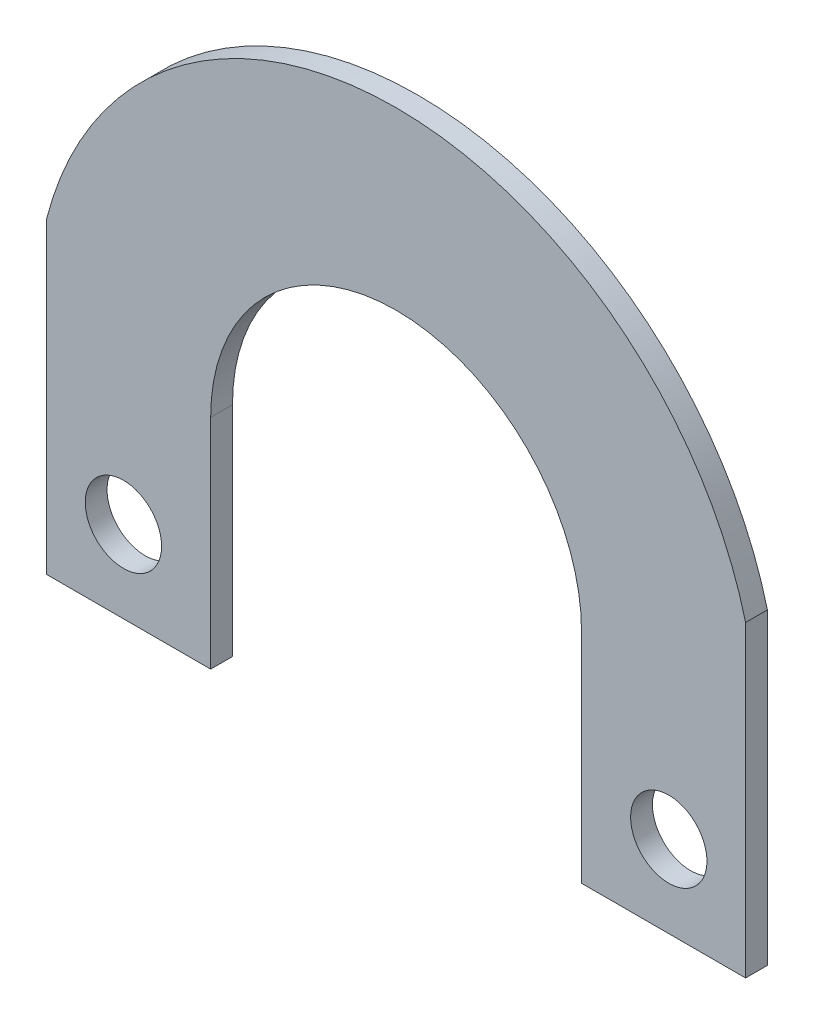
SolidWorks part; units mm, degrees
ref_plane "Front Plane" through (0, 0, 0) normal (0, 0, 1) x (1, 0, 0)
ref_plane "Top Plane" through (0, 0, 0) normal (0, 1, 0) x (1, 0, 0)
ref_plane "Right Plane" through (0, 0, 0) normal (1, 0, 0) x (0, 0, -1)
sketch "Sketch1" plane through (0, 0, 0) normal (0, 0, 1) x (1, 0, 0)
  line L73 (-17.5, -20) -> (-32.0429, -20)
  line L76 (17.5, -20) -> (32.0429, -20)
  line L79 (-17, 0) -> (17, 0) construction
  line L82 (0, 16.1073) -> (0, -16.1073) construction
  line L83 (32.0429, -20) -> (32.0429, 8.2281)
  line L84 (-25, -12.5) -> (25, -12.5) construction
  line L85 (-32.0429, -20) -> (-32.0429, 8.2281)
  line L86 (-48.3331, 30.2145) -> (-13.6202, 10.173)
  line L87 (13.6202, 10.173) -> (48.3331, 30.2145)
  line L90 (-17, 0) -> (-17, -20)
  line L91 (-17, -20) -> (-17.5, -20)
  line L95 (17, 0) -> (17, -20)
  line L96 (17, -20) -> (17.5, -20)
  circle A7 centre (-25, -12.5) radius 3.5
  circle A8 centre (25, -12.5) radius 3.5
  arc A11 (48.3331, 30.2145) -> (-48.3331, 30.2145) centre (0, 0) ccw
  arc A12 (13.6202, 10.173) -> (-13.6202, 10.173) centre (0, 0) ccw
  arc A14 (17, 0) -> (-17, 0) centre (0, 0) ccw
  arc A19 (32.0429, 8.2281) -> (-32.0429, 8.2281) centre (0, 0) ccw
  point P6 (32.0429, 14.5187)
  point P9 (32.0429, 20.8094)
  point P13 (-32.0429, 14.5187)
  point P15 (0, 0)
  dimension "D4" = 7
  dimension "D3" = 0
  dimension "D5" = 50
extrude "Boss-Extrude1" add sketch "Sketch1" along normal blind 2
